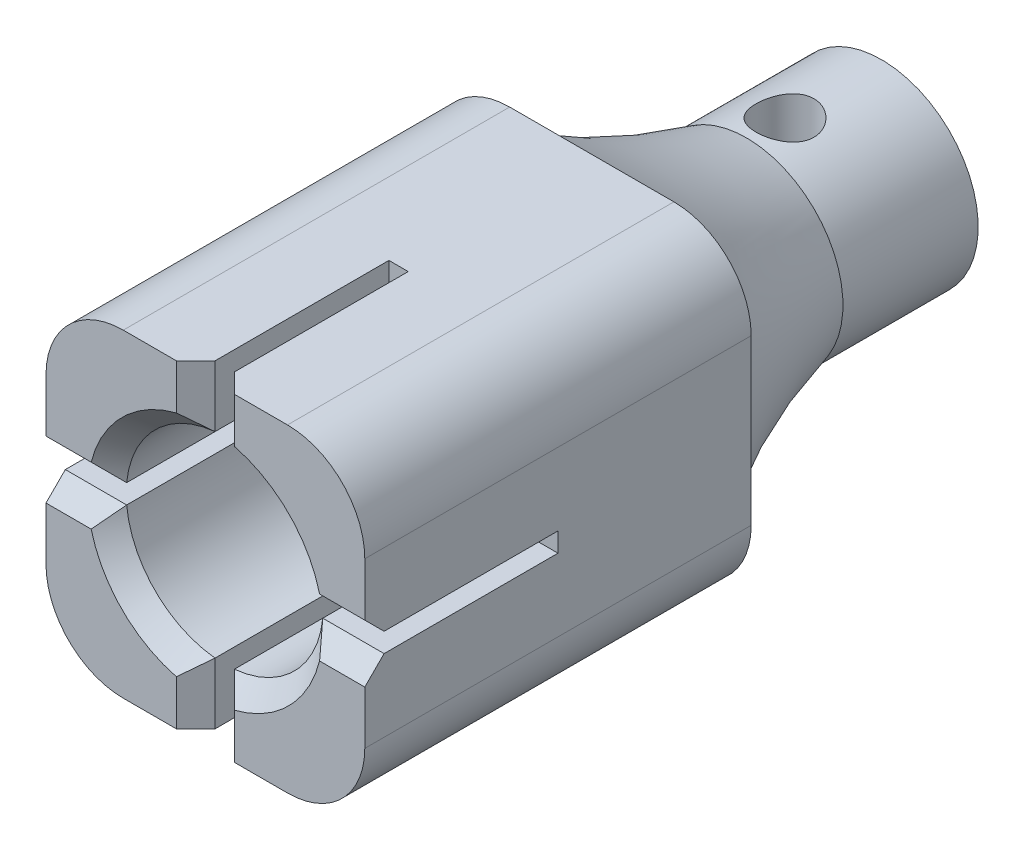
SolidWorks part; units mm, degrees
ref_plane "Front Plane" through (0, 0, 0) normal (0, 0, 1) x (1, 0, 0)
ref_plane "Top Plane" through (0, 0, 0) normal (0, 1, 0) x (1, 0, 0)
ref_plane "Right Plane" through (0, 0, 0) normal (1, 0, 0) x (0, 0, -1)
sketch "Sketch2" plane through (0, 0, 0) normal (0, 0, 1) x (1, 0, 0)
  line L1 (4.25, -8.25) -> (-4.25, -8.25)
  line L2 (8.25, -4.25) -> (8.25, 4.25)
  line L3 (4.25, 8.25) -> (-4.25, 8.25)
  line L4 (-8.25, -4.25) -> (-8.25, 4.25)
  line L5 (8.25, -8.25) -> (-8.25, 8.25) construction
  line L6 (8.25, 8.25) -> (-8.25, -8.25) construction
  arc A0 (-8.25, -4.25) -> (-4.25, -8.25) centre (-4.25, -4.25) ccw
  arc A1 (8.25, -4.25) -> (4.25, -8.25) centre (4.25, -4.25) cw
  arc A2 (4.25, 8.25) -> (8.25, 4.25) centre (4.25, 4.25) cw
  arc A3 (-4.25, 8.25) -> (-8.25, 4.25) centre (-4.25, 4.25) ccw
  point P0 (0, 0)
  dimension "D3" = 4
  dimension "D1" = 16.5
  dimension "D2" = 16.5
extrude "Boss-Extrude1" add sketch "Sketch2" along normal mid plane 20 contours L3 A3 L4 A0 L1 A1 L2 A2
sketch "Sketch10" plane through (0, 0, 0) normal (0, 0, 1) x (1, 0, 0)
  line L0 (0, 0) -> (0, 8.5657) construction
  line L1 (0, 0) -> (11.9886, 0) construction
  line L2 (0, 0) -> (10.1142, 10.1142) construction
  line L3 (0.5, 3) -> (-0.5, 3)
  line L4 (0.5, 3) -> (0.5, 13)
  line L5 (0.5, 13) -> (-0.5, 13)
  line L6 (-0.5, 3) -> (-0.5, 13)
  line L7 (0.5, 3) -> (-0.5, 13) construction
  line L8 (0.5, 13) -> (-0.5, 3) construction
  line L9 (3, -0.5) -> (13, -0.5)
  line L10 (3, 0.5) -> (3, -0.5)
  line L11 (3, 0.5) -> (13, 0.5)
  line L12 (13, 0.5) -> (13, -0.5)
  line L13 (0.5, -3) -> (-0.5, -3)
  line L14 (0.5, -3) -> (0.5, -13)
  line L15 (-0.5, -3) -> (-0.5, -13)
  line L16 (0.5, -13) -> (-0.5, -13)
  line L17 (-3, 0.5) -> (-3, -0.5)
  line L18 (-3, -0.5) -> (-13, -0.5)
  line L19 (-13, 0.5) -> (-13, -0.5)
  line L20 (-3, 0.5) -> (-13, 0.5)
  point P3 (0, 8)
  dimension "D1" = 1
  dimension "D2" = 10
  dimension "D3" = 8
  dimension "D4" = 45
sketch "Sketch12" plane through (0, 0, -10) normal (0, 0, -1) x (-1, 0, 0)
  circle A0 centre (0, 0) radius 5
  dimension "D1" = 10
extrude "Boss-Extrude3" add sketch "Sketch12" along normal blind 15
sketch "Sketch13" plane through (0, 0, -25) normal (0, 0, -1) x (-1, 0, 0)
  line L0 (-2.0767, 2.5) -> (2.0767, 2.5)
  arc A0 (-2.0767, 2.5) -> (2.0767, 2.5) centre (0, 0) ccw
  dimension "D1" = 6.5
  dimension "D2" = 2.5
extrude "Cut-Extrude3" cut sketch "Sketch13" against normal blind 40 contours L0 A0
sketch "Sketch14" plane through (0, 0, 0) normal (0, 1, 0) x (1, 0, 0)
  circle A0 centre (0, 20) radius 1.5
  point P0 (0, 0)
  point P8 (0, 0)
  dimension "D2" = 3
  dimension "D1" = 20
extrude "Cut-Extrude4" cut sketch "Sketch14" along normal blind 12 contours A0
chamfer "Chamfer5" distance 1 angle 45 2 edges at (0, 2.5, -25) (0, -3.25, -25)
extrude "Cut-Extrude5" cut sketch "Sketch10" along normal blind 25
sketch "Sketch16" plane through (0, 0, 0) normal (0, 0, 1) x (1, 0, 0)
  circle A0 centre (0, 0) radius 5.1
  dimension "D1" = 10.2
extrude "Cut-Extrude6" cut sketch "Sketch16" along normal blind 25 contours A0
sketch "Sketch56" plane through (0, 0, 0) normal (1, 0, 0) x (0, 0, -1)
  line L0 (10, 5) -> (10, 8.25)
  line L1 (10, 5) -> (18, 5)
  line L2 (18.5, 5) -> (10, 5) construction
  line L3 (0, 0) -> (38.0353, 0) construction
  arc A0 (10, 8.25) -> (18, 5) centre (25.1738, 34.1297) ccw
  dimension "D2" = 30
  dimension "D1" = 8
revolve "Revolve3" add sketch "Sketch56" angle 360 about L3
chamfer "Chamfer6" distance 1 angle 45 4 edges at (-3.6062, -3.6062, 10) (3.6062, -3.6062, 10) (3.6062, 3.6062, 10) (-3.6062, 3.6062, 10)
chamfer "Chamfer7" distance 1 angle 45 8 edges at (0.5, 7.1647, 10) (-0.5, 7.1647, 10) (-7.1647, 0.5, 10) (-7.1647, -0.5, 10) (-0.5, -7.1647, 10) (0.5, -7.1647, 10) (7.1647, -0.5, 10) (7.1647, 0.5, 10)
